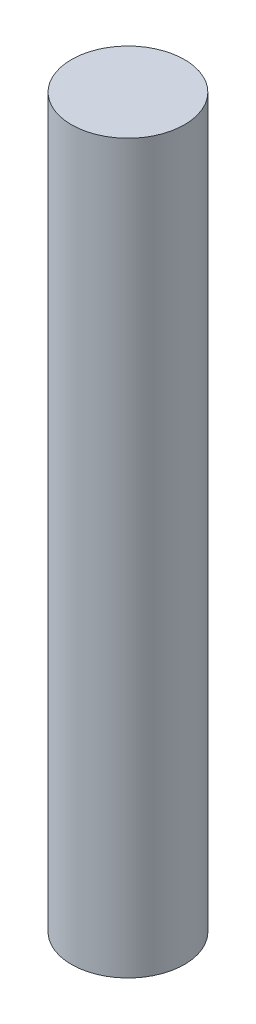
SolidWorks part; units mm, degrees
ref_plane "Front Plane" through (0, 0, 0) normal (0, 0, 1) x (1, 0, 0)
ref_plane "Top Plane" through (0, 0, 0) normal (0, 1, 0) x (1, 0, 0)
ref_plane "Right Plane" through (0, 0, 0) normal (1, 0, 0) x (0, 0, -1)
sketch "Sketch1" plane through (0, 0, 0) normal (0, 1, 0) x (1, 0, 0)
  circle A0 centre (0, 0) radius 36.5125
  dimension "D1" = 73.025
extrude "Boss-Extrude1" add sketch "Sketch1" along normal blind 469.9
